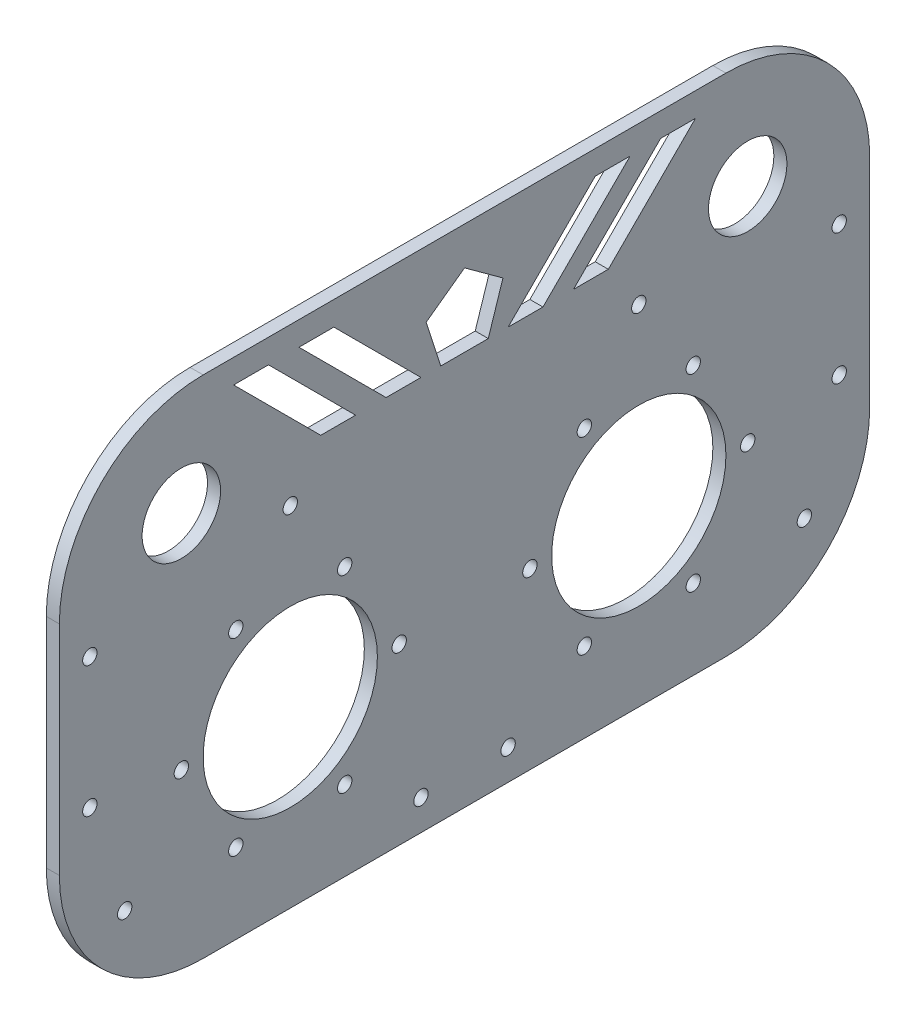
SolidWorks part; units mm, degrees
ref_plane "前视基准面" through (0, 0, 0) normal (0, 0, 1) x (1, 0, 0)
ref_plane "上视基准面" through (0, 0, 0) normal (0, 1, 0) x (1, 0, 0)
ref_plane "右视基准面" through (0, 0, 0) normal (1, 0, 0) x (0, 0, -1)
sketch "草图1" plane through (0, 0, 0) normal (1, 0, 0) x (0, 0, -1)
  line L0 (-60, -25) -> (60, -25) construction
  line L1 (60, -58) -> (-60, -58)
  line L2 (60, -58) -> (60, 58)
  line L3 (60, 58) -> (-60, 58)
  line L4 (-60, -58) -> (-60, 58)
  line L5 (60, -58) -> (-60, 58) construction
  line L6 (60, 58) -> (-60, -58) construction
  line L7 (-60, 25) -> (60, 25)
  line L8 (-93, 25) -> (-93, -25)
  line L9 (93, 25) -> (93, -25)
  arc A0 (60, -58) -> (93, -25) centre (60, -25) ccw
  arc A1 (-60, -58) -> (-93, -25) centre (-60, -25) cw
  arc A2 (-60, 58) -> (-93, 25) centre (-60, 25) ccw
  arc A3 (60, 58) -> (93, 25) centre (60, 25) cw
  point P0 (0, 0)
  dimension "D1" = 120
  dimension "D2" = 116
  dimension "D3" = 33
  dimension "D4" = 33
extrude "凸台-拉伸2" add sketch "草图1" along normal blind 3 contours L7 L4 L1 L2 | L4 L7 L2 L3 | L4 A2 L8 A1 | A3 L2 A0 L9
sketch "草图2" plane through (3, 0, 0) normal (1, 0, 0) x (0, 0, -1)
  line L0 (0, 0) -> (93, 0) construction
  line L1 (0, -18) -> (-40, -18)
  line L2 (-40, -18) -> (-40, 2) construction
  line L3 (0, -58) -> (0, 22) construction
  line L4 (-40, 22) -> (40, 22) construction
  line L5 (0, 0) -> (0, -58) construction
  line L6 (0, -58) -> (0, -18)
  line L7 (0, -18) -> (40, -18)
  line L8 (40, -18) -> (40, 2) construction
  circle A0 centre (40, -18) radius 20
  circle A1 centre (-40, -18) radius 20
  circle A2 centre (-40, -18) radius 25 construction
  circle A3 centre (40, -18) radius 25 construction
  circle A17 centre (-65, -18) radius 1.65
  circle A19 centre (-52.5, 3.6506) radius 1.65
  circle A20 centre (-27.5, 3.6506) radius 1.65
  circle A21 centre (-15, -18) radius 1.65
  circle A22 centre (-27.5, -39.6506) radius 1.65
  circle A23 centre (-52.5, -39.6506) radius 1.65
  circle A24 centre (65, -18) radius 1.65
  circle A25 centre (52.5, -39.6506) radius 1.65
  circle A26 centre (27.5, -39.6506) radius 1.65
  circle A27 centre (15, -18) radius 1.65
  circle A28 centre (27.5, 3.6506) radius 1.65
  circle A29 centre (52.5, 3.6506) radius 1.65
  circle A31 centre (-40, 22) radius 1.65
  circle A32 centre (40, 22) radius 1.65
  dimension "D5" = 40
  dimension "D6" = 40
  dimension "D7" = 40
  dimension "D8" = 50
  dimension "D9" = 50
  dimension "D12" = 6
  dimension "D13" = 6
  dimension "D14" = 80
  dimension "D15" = 3.3
  dimension "D10" = 3.3
  dimension "D11" = 3.3
  dimension "D16" = 3.3
  dimension "D1" = 93
  dimension "D2" = 58
  dimension "D3" = 40
  dimension "D4" = 40
extrude "切除-拉伸1" cut sketch "草图2" against normal blind 3 contours A23 | A0 | A1 | A19 | A17 | A22 | A21 | A27 | A28 | A29 | A24 | A25 | A26 | A20 | A31 | A32
sketch "草图3" plane through (3, 0, 0) normal (1, 0, 0) x (0, 0, -1)
  line L0 (0, -58) -> (-10, -58)
  line L1 (60, -58) -> (-60, -58) construction
  line L2 (0, -58) -> (10, -58)
  line L3 (-10, -58) -> (-10, -51)
  line L4 (10, -58) -> (10, -51)
  circle A0 centre (-10, -51) radius 1.65
  circle A1 centre (10, -51) radius 1.65
  dimension "D5" = 3.3
  dimension "D6" = 3.3
  dimension "D1" = 10
  dimension "D2" = 10
  dimension "D3" = 7
  dimension "D4" = 7
extrude "切除-拉伸2" cut sketch "草图3" against normal blind 10 contours A0 | A1
sketch "草图4" plane through (0, 0, 0) normal (-1, 0, 0) x (0, 0, 1)
  line L0 (93, 0) -> (93, -15)
  line L1 (93, 25) -> (93, -25) construction
  line L2 (93, -15) -> (86, -15)
  line L3 (93, 0) -> (93, 15)
  line L4 (93, 15) -> (86, 15)
  line L5 (-93, 0) -> (-93, -15)
  line L6 (-93, 25) -> (-93, -25) construction
  line L7 (-93, 0) -> (-93, 15)
  line L8 (-93, 15) -> (-86, 15)
  line L9 (-93, -15) -> (-86, -15)
  circle A1 centre (86, 15) radius 1.65
  circle A2 centre (86, -15) radius 1.65
  circle A3 centre (-86, 15) radius 1.65
  circle A4 centre (-86, -15) radius 1.65
  dimension "D5" = 3.3
  dimension "D6" = 3.3
  dimension "D11" = 3.3
  dimension "D12" = 3.3
  dimension "D1" = 15
  dimension "D2" = 7
  dimension "D3" = 15
  dimension "D4" = 7
  dimension "D7" = 15
  dimension "D8" = 15
  dimension "D9" = 7
  dimension "D10" = 7
extrude "切除-拉伸3" cut sketch "草图4" against normal blind 5 contours A1 | A2 | A4 | A3
sketch "草图6" plane through (0, 0, 0) normal (-1, 0, 0) x (0, 0, 1)
  line L0 (0, 0) -> (0, 40) construction
  line L1 (0, 40) -> (-45, 40) construction
  line L2 (0, 40) -> (45, 40) construction
  line L3 (-25, 32.5) -> (-33, 32.5)
  line L4 (0, 49.2705) -> (-8.8168, 42.8647)
  line L5 (-8.8168, 42.8647) -> (-5.4491, 32.5)
  line L6 (-5.4491, 32.5) -> (5.4491, 32.5)
  line L7 (5.4491, 32.5) -> (8.8168, 42.8647)
  line L8 (8.8168, 42.8647) -> (0, 49.2705)
  line L9 (-33, 32.5) -> (-53, 52.5)
  line L10 (-53, 52.5) -> (-45, 52.5)
  line L11 (-45, 52.5) -> (-25, 32.5)
  line L12 (-10, 32.5) -> (-18, 32.5)
  line L13 (-18, 32.5) -> (-38, 52.5)
  line L14 (-38, 52.5) -> (-30, 52.5)
  line L15 (-30, 52.5) -> (-10, 32.5)
  line L16 (38, 52.5) -> (30, 52.5)
  line L17 (18, 32.5) -> (38, 52.5)
  line L18 (10, 32.5) -> (18, 32.5)
  line L19 (30, 52.5) -> (10, 32.5)
  line L20 (53, 52.5) -> (45, 52.5)
  line L21 (33, 32.5) -> (53, 52.5)
  line L22 (25, 32.5) -> (33, 32.5)
  line L23 (45, 52.5) -> (25, 32.5)
  circle A0 centre (0, 40) radius 7.5 construction
  dimension "D4" = 15
  dimension "D1" = 40
  dimension "D2" = 45
  dimension "D3" = 45
  dimension "D5" = 8
  dimension "D6" = 20
  dimension "D7" = 8
  dimension "D8" = 8
  dimension "D9" = 135
  dimension "D10" = 135
  dimension "D11" = 20
  dimension "D12" = 10
  dimension "D13" = 25
  dimension "D14" = 8
extrude "切除-拉伸6" cut sketch "草图6" against normal blind 3
sketch "草图8" plane through (3, 0, 0) normal (1, 0, 0) x (0, 0, -1)
  line L0 (0, -58) -> (0, -43.5) construction
  line L1 (60, -58) -> (-60, -58) construction
  line L2 (93, 25) -> (93, -25) construction
  circle A0 centre (78, -39.5) radius 1.65
  circle A2 centre (-78, -39.5) radius 1.65
  dimension "D2" = 3.3
  dimension "D1" = 14.5
  dimension "D3" = 18.5
  dimension "D4" = 15
sketch "草图9" plane through (0, 0, 0) normal (-1, 0, 0) x (0, 0, 1)
  line L1 (-80.5, -42) -> (-75.5, -42)
  line L2 (-80.5, -42) -> (-80.5, -37)
  line L3 (-80.5, -37) -> (-75.5, -37)
  line L4 (-75.5, -42) -> (-75.5, -37)
  line L5 (-80.5, -42) -> (-75.5, -37) construction
  line L6 (-80.5, -37) -> (-75.5, -42) construction
  line L7 (75.5, -42) -> (80.5, -42)
  line L8 (75.5, -42) -> (75.5, -37)
  line L9 (75.5, -37) -> (80.5, -37)
  line L10 (80.5, -42) -> (80.5, -37)
  line L11 (75.5, -42) -> (80.5, -37) construction
  line L12 (75.5, -37) -> (80.5, -42) construction
  point P0 (-78, -39.5)
  point P6 (78, -39.5)
  dimension "D1" = 5
  dimension "D2" = 5
  dimension "D3" = 5
  dimension "D4" = 5
extrude "凸台-拉伸4" add sketch "草图9" along normal blind 2.25
extrude "切除-拉伸9" cut sketch "草图8" against normal blind 7
sketch "草图11" plane through (3, 0, 0) normal (1, 0, 0) x (0, 0, -1)
  line L0 (60, 58) -> (-60, 58) construction
  line L1 (0, 0) -> (0, 58) construction
  circle A0 centre (-65, 33) radius 9
  circle A3 centre (65, 33) radius 9
  dimension "D2" = 18
  dimension "D3" = 25
  dimension "D4" = 65
extrude "切除-拉伸10" cut sketch "草图11" against normal blind 10
